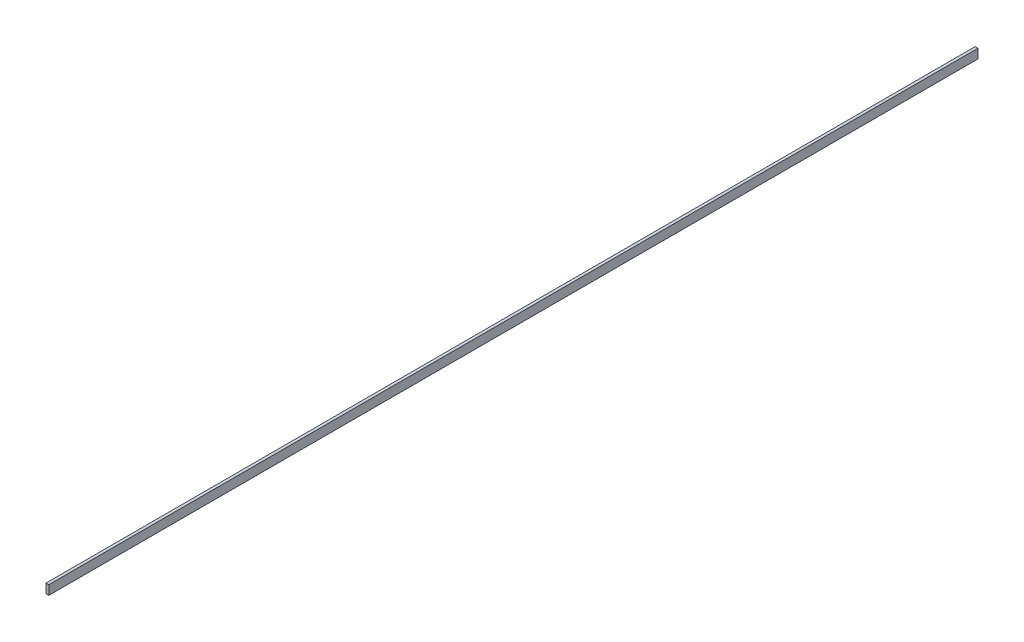
SolidWorks part; units mm, degrees
ref_plane "Front Plane" through (0, 0, 0) normal (0, 0, 1) x (1, 0, 0)
ref_plane "Top Plane" through (0, 0, 0) normal (0, 1, 0) x (1, 0, 0)
ref_plane "Right Plane" through (0, 0, 0) normal (1, 0, 0) x (0, 0, -1)
sketch "Sketch2" plane through (0, 0, 0) normal (0, 0, 1) x (1, 0, 0)
  line L1 (0, 0) -> (3, 0)
  line L2 (0, 0) -> (0, -10)
  line L3 (0, -10) -> (3, -10)
  line L4 (3, 0) -> (3, -10)
  dimension "D1" = 3
  dimension "D2" = 10
extrude "Boss-Extrude1" add sketch "Sketch2" against normal blind 1000
